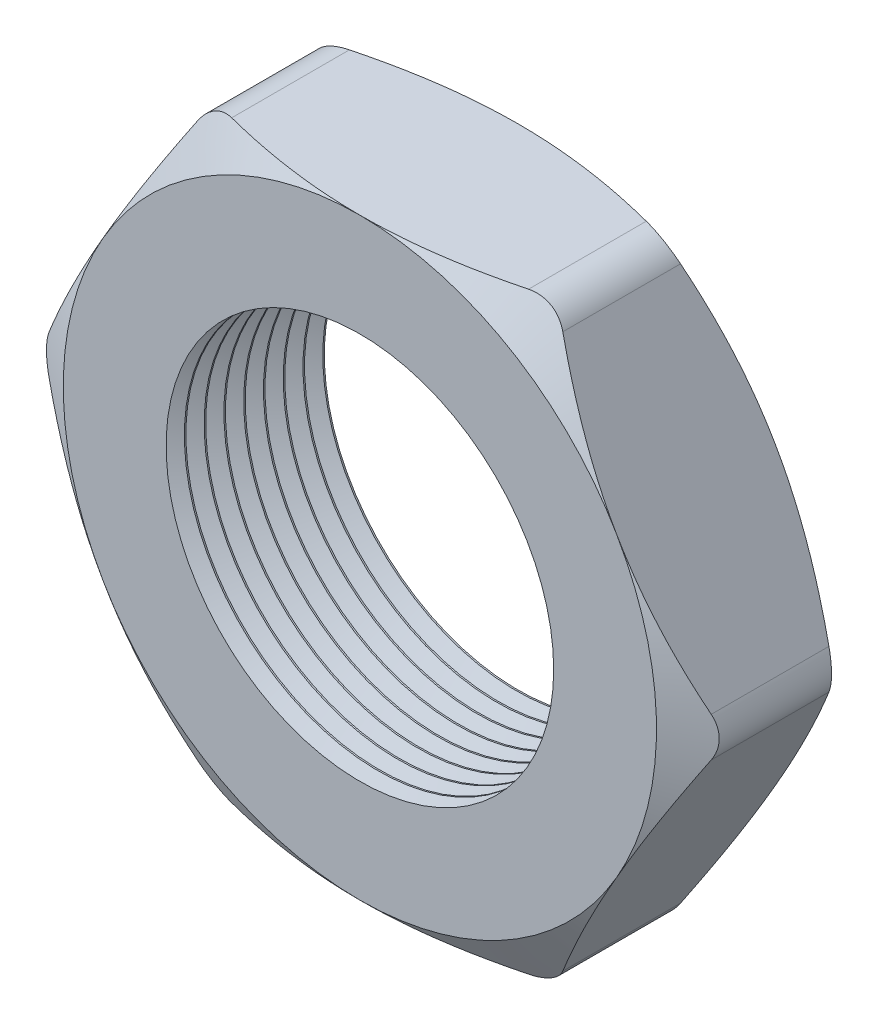
SolidWorks part; units mm, degrees
ref_plane "Front Plane" through (0, 0, 0) normal (0, 0, 1) x (1, 0, 0)
ref_plane "Top Plane" through (0, 0, 0) normal (0, 1, 0) x (1, 0, 0)
ref_plane "Right Plane" through (0, 0, 0) normal (1, 0, 0) x (0, 0, -1)
sketch "Sketch1" plane through (0, 0, 0) normal (0, 0, 1) x (1, 0, 0)
  line L1 (-10.9985, 0) -> (-5.4993, -9.525)
  line L2 (-5.4993, -9.525) -> (5.4993, -9.525)
  line L3 (5.4993, -9.525) -> (10.9985, 0)
  line L4 (10.9985, 0) -> (5.4993, 9.525)
  line L5 (5.4993, 9.525) -> (-5.4993, 9.525)
  line L6 (-5.4993, 9.525) -> (-10.9985, 0)
  circle A0 centre (0, 0) radius 9.525 construction
  circle A1 centre (0, 0) radius 6.223
  dimension "TS" = 12.446
  dimension "H" = 19.05
extrude "Extrude1" add sketch "Sketch1" along normal blind 5.08
sketch "Sketch2" plane through (0, 0, 5.08) normal (0, 0, 1) x (1, 0, 0)
  line L0 (5.4993, 9.525) -> (-5.4993, 9.525) construction
  circle A0 centre (0, 0) radius 9.525
extrude "Cut-Extrude1" cut sketch "Sketch2" against normal through all draft 60 flip side to cut
sketch "Sketch3" plane through (0, 0, 0) normal (0, 0, -1) x (-1, 0, 0)
  line L0 (-5.4993, 9.525) -> (5.4993, 9.525) construction
  circle A0 centre (0, 0) radius 9.525
extrude "Cut-Extrude2" cut sketch "Sketch3" against normal through all draft 60 flip side to cut
fillet "Fillet1" radius 1.27 6 edges at (10.9985, 0, 2.54) (5.4993, -9.525, 2.54) (-5.4993, -9.525, 2.54) (-10.9985, 0, 2.54) (-5.4993, 9.525, 2.54) (5.4993, 9.525, 2.54)
sketch "Sketch4" plane through (0, 0, 0) normal (0, 1, 0) x (1, 0, 0)
  line L0 (-6.223, -5.08) -> (-6.223, -4.4934)
  line L1 (-6.223, 0) -> (-6.223, -5.08) construction
  line L2 (-6.223, -4.4934) -> (-6.731, -4.7867)
  line L3 (-6.731, -4.7867) -> (-6.223, -5.08)
  dimension "D1" = 60
  dimension "D2" = 60
  dimension "D3" = 0.508
revolve "Cut-Revolve1" cut sketch "Sketch4" angle 360 about axis through (0, 0, 0) along (0, 0, 1)
pattern_linear "LPattern1" count 8 spacing 0.635 along (0, 0, -1) of "Cut-Revolve1"
